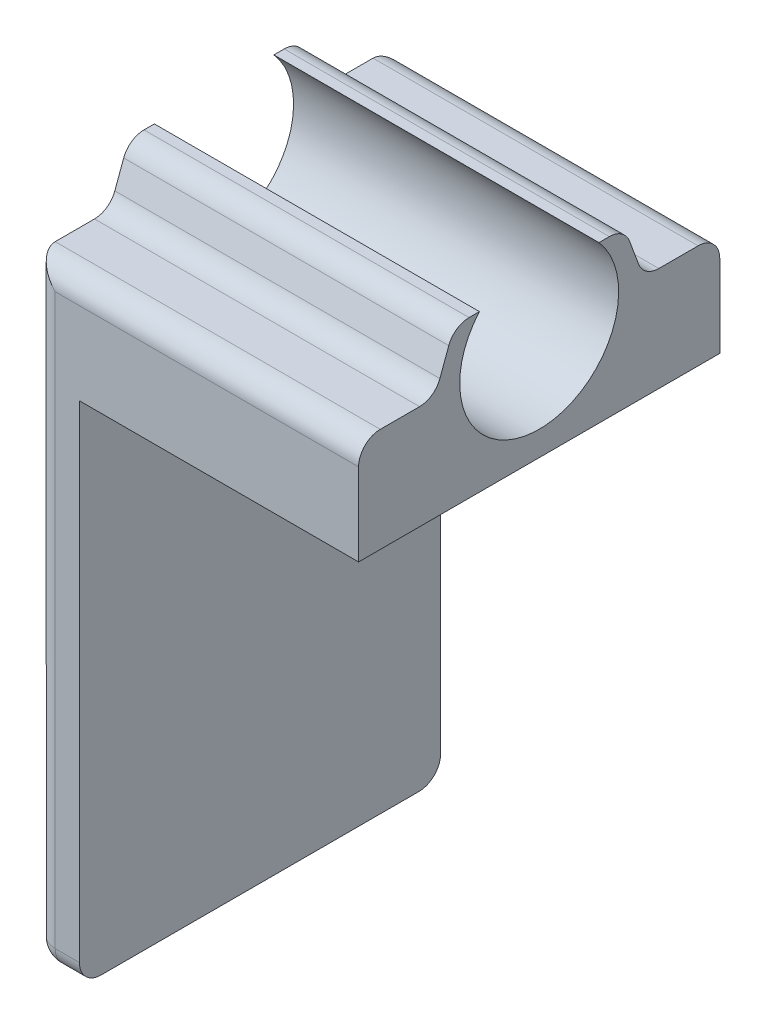
SolidWorks part; units mm, degrees
ref_plane "Front Plane" through (0, 0, 0) normal (0, 0, 1) x (1, 0, 0)
ref_plane "Top Plane" through (0, 0, 0) normal (0, 1, 0) x (1, 0, 0)
ref_plane "Right Plane" through (0, 0, 0) normal (1, 0, 0) x (0, 0, -1)
sketch "Sketch1" plane through (0, 0, 0) normal (0, 1, 0) x (1, 0, 0)
  line L1 (-22.5, -25) -> (22.5, -25)
  line L2 (-22.5, -25) -> (-22.5, 25)
  line L3 (-22.5, 25) -> (22.5, 25)
  line L4 (22.5, -25) -> (22.5, 25)
  line L5 (-22.5, -25) -> (22.5, 25) construction
  line L6 (-22.5, 25) -> (22.5, -25) construction
  point P0 (0, 0)
  dimension "D1" = 45
  dimension "D2" = 50
extrude "Boss-Extrude1" add sketch "Sketch1" along normal blind 92
sketch "Sketch2" plane through (0, 0, -25) normal (0, 0, -1) x (-1, 0, 0)
  line L0 (-22.5, 92) -> (-22.5, 0) construction
  line L1 (-22.5, 0) -> (16.15, 0)
  line L2 (-22.5, 0) -> (-22.5, 70.35)
  line L3 (-22.5, 70.35) -> (16.15, 70.35)
  line L4 (16.15, 0) -> (16.15, 70.35)
  line L5 (-22.5, 0) -> (22.5, 0) construction
  line L6 (22.5, 92) -> (22.5, 0) construction
  dimension "D1" = 0
  dimension "D2" = 6.35
  dimension "D3" = 70.35
sketch "Sketch3" plane through (22.5, 0, 0) normal (1, 0, 0) x (0, 0, -1)
  line L0 (0, 92) -> (0, 77.5) construction
  line L1 (-25, 92) -> (25, 92) construction
  circle A0 centre (0, 84.75) radius 11
  dimension "D1" = 22
  dimension "D2" = 7.25
extrude "Cut-Extrude2" cut sketch "Sketch3" against normal up to surface (45 mm away) up to face at (-22.5, 46, 0)
sketch "Sketch4" plane through (22.5, 0, 0) normal (1, 0, 0) x (0, 0, -1)
  line L0 (11.793, 92) -> (14.47, 84.75)
  line L1 (25, 92) -> (25, 0) construction
  line L2 (25, 84.75) -> (-25, 84.75) construction
  line L3 (-25, 92) -> (-25, 0) construction
  line L4 (8.2727, 92) -> (25, 92) construction
  line L5 (14.47, 84.75) -> (25, 84.75)
  line L6 (25, 84.75) -> (25, 92)
  line L7 (25, 92) -> (11.793, 92)
  line L8 (0, 84.75) -> (0, 92) construction
  line L9 (-25, 84.75) -> (-25, 92)
  line L10 (-14.47, 84.75) -> (-25, 84.75)
  line L11 (-11.793, 92) -> (-14.47, 84.75)
  line L12 (-25, 92) -> (-11.793, 92)
extrude "Cut-Extrude3" cut sketch "Sketch4" against normal up to surface (45 mm away) up to face at (-22.5, 58.2917, 0)
fillet "Fillet5" radius 3 4 edges at (0, 84.75, 14.47) (0, 92, 11.793) (0, 84.75, -14.47) (0, 92, -11.793)
fillet "Fillet6" radius 3 8 edges at (22.5, 0, 0) (0, 0, -25) (0, 0, 25) (-22.5, 0, 0) (0, 84.75, -25) (0, 84.75, 25) (-22.5, 42.375, 25) (-22.5, 42.375, -25)
sketch "Sketch5" plane through (-22.5, 0, 0) normal (-1, 0, 0) x (0, 0, 1)
  line L0 (-19.5199, 8.015) -> (19.2476, 8.015) construction
  text T0 "OneChair V3"
extrude "Cut-Extrude4" cut sketch "Sketch5" against normal blind 1
sketch "Sketch15" plane through (-22.5, 0, 0) normal (-1, 0, 0) x (0, 0, 1)
  line L3 (10.2596, 32.0046) -> (9.9115, 31.8204)
  line L7 (10.2596, 30.9578) -> (10.2596, 30.6198)
  line L10 (12.867, 34.9608) -> (4.2649, 30.6858)
  line L11 (14.52, 34.2529) -> (10.2596, 32.0046)
  line L12 (10.2596, 32.0046) -> (9.9115, 31.8204)
  line L13 (9.9115, 31.8204) -> (-14.2582, 18.9772)
  line L14 (-11.8535, 18.0077) -> (-8.8687, 18.0077)
  line L15 (10.2596, 30.0222) -> (10.2596, 30.9578)
  line L16 (10.828, 30.7106) -> (10.828, 30.7064)
  spline S7 degree 3 poles (-15.2979, 21.0019) (-15.3375, 21.2141) (-15.3567, 21.4299) (-15.3849, 21.6442) knots 29 29 29 29 30 30 30 30
  spline S8 degree 3 poles (-15.1435, 20.3562) (-15.1984, 20.5822) (-15.2583, 20.7902) (-15.2979, 21.0019) knots 28 28 28 28 29 29 29 29
  spline S9 degree 3 poles (-10.0647, 23.0588) (-11.7426, 22.1659) (-13.4314, 21.2673) (-15.1435, 20.3562) knots 27 27 27 27 28 28 28 28
  spline S10 degree 3 poles (-10.1505, 23.6586) (-10.1362, 23.4613) (-10.0952, 23.2658) (-10.0647, 23.0588) knots 26 26 26 26 27 27 27 27
  spline S11 degree 3 poles (-10.0043, 24.7775) (-10.1119, 24.4127) (-10.1781, 24.0401) (-10.1505, 23.6586) knots 25 25 25 25 26 26 26 26
  spline S12 degree 3 poles (-9.1188, 27.7673) (-9.4119, 26.7701) (-9.7102, 25.7744) (-10.0043, 24.7775) knots 24 24 24 24 25 25 25 25
  spline S13 degree 3 poles (-8.585, 28.698) (-8.8238, 28.4241) (-9.0148, 28.1212) (-9.1188, 27.7673) knots 23 23 23 23 24 24 24 24
  spline S14 degree 3 poles (-6.5207, 30.0144) (-7.3559, 29.8102) (-8.0265, 29.3386) (-8.585, 28.698) knots 22 22 22 22 23 23 23 23
  spline S15 degree 3 poles (-5.8867, 30.0896) (-6.0986, 30.0862) (-6.3152, 30.0646) (-6.5207, 30.0144) knots 21 21 21 21 22 22 22 22
  spline S16 degree 3 poles (-3.9427, 30.0956) (-4.5907, 30.095) (-5.2388, 30.0998) (-5.8867, 30.0896) knots 20 20 20 20 21 21 21 21
  spline S17 degree 3 poles (0.0807, 30.0993) (-1.2605, 30.097) (-2.6016, 30.0969) (-3.9427, 30.0956) knots 19 19 19 19 20 20 20 20
  spline S18 degree 3 poles (2.8334, 30.103) (1.916, 30.114) (0.9983, 30.1009) (0.0807, 30.0993) knots 18 18 18 18 19 19 19 19
  spline S19 degree 3 poles (3.4965, 30.2699) (3.284, 30.1558) (3.0781, 30.1) (2.8334, 30.103) knots 17 17 17 17 18 18 18 18
  spline S28 degree 3 poles (-12.5035, 30.7783) (-11.8211, 31.7697) (-10.94, 32.5326) (-9.8566, 33.0581) knots 5 5 5 5 6 6 6 6
  spline S29 degree 3 poles (-13.5209, 28.6858) (-13.2999, 29.4445) (-12.9836, 30.15) (-12.5035, 30.7783) knots 4 4 4 4 5 5 5 5
  spline S30 degree 3 poles (-15.205, 22.9992) (-14.6499, 24.8966) (-14.074, 26.7879) (-13.5209, 28.6858) knots 3 3 3 3 4 4 4 4
  spline S31 degree 3 poles (-15.3675, 22.092) (-15.3147, 22.3949) (-15.2907, 22.706) (-15.205, 22.9992) knots 2 2 2 2 3 3 3 3
  spline S32 degree 3 poles (-15.3849, 22.0015) (-15.3791, 22.0317) (-15.3728, 22.0618) (-15.3675, 22.092) knots 1 1 1 1 2 2 2 2
  spline S33 degree 3 poles (-15.3849, 21.6442) (-15.3849, 21.7633) (-15.3849, 21.8824) (-15.3849, 22.0015) knots 0 0 0 0 1 1 1 1
  spline S35 degree 3 poles (9.9115, 31.8204) (1.8611, 27.5421) (-6.186, 23.2664) (-14.2582, 18.9772) knots 3 3 3 3 4 4 4 4
  spline S36 degree 3 poles (-14.2582, 18.9772) (-14.0985, 18.8485) (-13.9614, 18.7241) (-13.8109, 18.6198) knots 4 4 4 4 5 5 5 5
  spline S37 degree 3 poles (-13.8109, 18.6198) (-13.2728, 18.2448) (-12.6632, 18.08) (-12.0175, 18.0287) knots 5 5 5 5 6 6 6 6
  spline S38 degree 3 poles (-12.0175, 18.0287) (-11.9629, 18.0245) (-11.9082, 18.0144) (-11.8535, 18.0077) knots 6 6 6 6 7 7 7 7
  spline S39 degree 3 poles (-15.3849, 21.6442) (-15.3563, 21.4298) (-15.3378, 21.2137) (-15.2975, 21.0018) knots 9 9 9 9 10 10 10 10
  spline S40 degree 3 poles (-15.2975, 21.0018) (-15.258, 20.7899) (-15.1983, 20.5822) (-15.1436, 20.3561) knots 10 10 10 10 11 11 11 11
  spline S41 degree 3 poles (-15.1436, 20.3561) (-13.4317, 21.2675) (-11.7426, 22.1663) (-10.0643, 23.0584) knots 11 11 11 11 12 12 12 12
  spline S42 degree 3 poles (-10.0643, 23.0584) (-10.0954, 23.2661) (-10.1366, 23.4612) (-10.1501, 23.6588) knots 12 12 12 12 13 13 13 13
  spline S43 degree 3 poles (-10.1501, 23.6588) (-10.1778, 24.0405) (-10.1122, 24.4129) (-10.0046, 24.7779) knots 13 13 13 13 14 14 14 14
  spline S44 degree 3 poles (-10.0046, 24.7779) (-9.7103, 25.7742) (-9.4119, 26.7697) (-9.1184, 27.7669) knots 14 14 14 14 15 15 15 15
  spline S45 degree 3 poles (-9.1184, 27.7669) (-9.015, 28.1209) (-8.8241, 28.4244) (-8.5853, 28.6977) knots 15 15 15 15 16 16 16 16
  spline S46 degree 3 poles (-8.5853, 28.6977) (-8.0262, 29.3384) (-7.3561, 29.8101) (-6.5203, 30.0144) knots 16 16 16 16 17 17 17 17
  spline S47 degree 3 poles (-6.5203, 30.0144) (-6.3152, 30.0648) (-6.0982, 30.0859) (-5.8864, 30.0892) knots 17 17 17 17 18 18 18 18
  spline S48 degree 3 poles (-5.8864, 30.0892) (-5.2389, 30.1002) (-4.5907, 30.0951) (-3.9424, 30.096) knots 18 18 18 18 19 19 19 19
  spline S49 degree 3 poles (-3.9424, 30.096) (-2.6013, 30.0968) (-1.2602, 30.0968) (0.0808, 30.0993) knots 19 19 19 19 20 20 20 20
  spline S50 degree 3 poles (0.0808, 30.0993) (0.9982, 30.101) (1.9163, 30.1144) (2.8336, 30.1027) knots 20 20 20 20 21 21 21 21
  spline S51 degree 3 poles (2.8336, 30.1027) (3.0783, 30.1002) (3.2843, 30.1556) (3.4962, 30.27) knots 21 21 21 21 22 22 22 22
  spline S52 degree 3 poles (3.4962, 30.27) (3.7524, 30.4092) (4.0087, 30.5475) (4.2649, 30.6858) knots 22 22 22 22 23 23 23 23
  spline S62 degree 3 poles (-15.3675, 22.092) (-15.3728, 22.0618) (-15.3791, 22.0317) (-15.3849, 22.0015) knots 9 9 9 9 10 10 10 10
  spline S63 degree 3 poles (-15.205, 22.9992) (-15.2907, 22.706) (-15.3147, 22.3949) (-15.3675, 22.092) knots 8 8 8 8 9 9 9 9
  spline S64 degree 3 poles (-13.5209, 28.6858) (-14.074, 26.7879) (-14.6499, 24.8966) (-15.205, 22.9992) knots 7 7 7 7 8 8 8 8
  spline S65 degree 3 poles (-12.5035, 30.7783) (-12.9836, 30.15) (-13.2999, 29.4445) (-13.5209, 28.6858) knots 6 6 6 6 7 7 7 7
  spline S66 degree 3 poles (-9.8566, 33.0581) (-10.94, 32.5326) (-11.8211, 31.7697) (-12.5035, 30.7783) knots 5 5 5 5 6 6 6 6
  spline S69 degree 3 poles (-8.8687, 18.0077) (-8.8317, 18.0127) (-8.7939, 18.0212) (-8.7569, 18.0212) knots 2 2 2 2 3 3 3 3
  spline S70 degree 3 poles (-8.7569, 18.0212) (-7.4225, 18.0228) (-6.0881, 18.0237) (-4.7538, 18.0254) knots 3 3 3 3 4 4 4 4
  spline S71 degree 3 poles (-4.7538, 18.0254) (-3.3286, 18.027) (-1.9035, 18.0279) (-0.4783, 18.0304) knots 4 4 4 4 5 5 5 5
  spline S72 degree 3 poles (-0.4783, 18.0304) (0.4987, 18.0321) (1.4757, 18.0338) (2.4527, 18.0388) knots 5 5 5 5 6 6 6 6
  spline S73 degree 3 poles (2.4527, 18.0388) (2.9118, 18.0413) (3.344, 18.175) (3.7627, 18.3491) knots 6 6 6 6 7 7 7 7
  spline S74 degree 3 poles (3.7627, 18.3491) (5.2963, 18.9872) (6.5576, 19.9735) (7.5253, 21.3255) knots 7 7 7 7 8 8 8 8
  spline S75 degree 3 poles (7.5253, 21.3255) (7.9466, 21.9132) (8.1921, 22.5808) (8.393, 23.272) knots 8 8 8 8 9 9 9 9
  spline S76 degree 3 poles (8.393, 23.272) (8.7991, 24.6694) (9.2229, 26.0618) (9.6341, 27.4575) knots 9 9 9 9 10 10 10 10
  spline S77 degree 3 poles (9.6341, 27.4575) (9.8098, 28.052) (9.9788, 28.6472) (10.1352, 29.2467) knots 10 10 10 10 11 11 11 11
  spline S78 degree 3 poles (10.1352, 29.2467) (10.1924, 29.4653) (10.2066, 29.6949) (10.2403, 29.9202) knots 11 11 11 11 12 12 12 12
  spline S79 degree 3 poles (10.2403, 29.9202) (10.2453, 29.9505) (10.2529, 29.9799) (10.2596, 30.0102) knots 12 12 12 12 13 13 13 13
  spline S80 degree 3 poles (-3.0486, 22.1503) (-0.3135, 24.0615) (2.4216, 25.9735) (5.1845, 27.9048) knots 8 8 8 8 9 9 9 9
  spline S81 degree 3 poles (-3.0369, 22.1293) (-3.0411, 22.1361) (-3.0444, 22.1428) (-3.0486, 22.1503) knots 7 7 7 7 8 8 8 8
  spline S82 degree 3 poles (-2.9957, 22.1276) (-3.0091, 22.1276) (-3.0234, 22.1285) (-3.0369, 22.1293) knots 6 6 6 6 7 7 7 7
  spline S83 degree 3 poles (1.2899, 22.1361) (-0.1386, 22.1243) (-1.5671, 22.1293) (-2.9957, 22.1276) knots 5 5 5 5 6 6 6 6
  spline S84 degree 3 poles (3.2196, 22.8306) (2.6587, 22.3774) (2.0088, 22.1428) (1.2899, 22.1361) knots 4 4 4 4 5 5 5 5
  spline S85 degree 3 poles (4.057, 24.0926) (3.8897, 23.6016) (3.629, 23.161) (3.2196, 22.8306) knots 3 3 3 3 4 4 4 4
  spline S86 degree 3 poles (4.4757, 25.4572) (4.3395, 25.0015) (4.21, 24.5424) (4.057, 24.0926) knots 2 2 2 2 3 3 3 3
  spline S87 degree 3 poles (5.145, 27.7106) (4.9222, 26.9598) (4.7002, 26.2081) (4.4757, 25.4572) knots 1 1 1 1 2 2 2 2
  spline S88 degree 3 poles (5.1845, 27.9048) (5.1677, 27.8207) (5.1601, 27.7644) (5.145, 27.7106) knots 0 0 0 0 1 1 1 1
  spline S93 degree 3 poles (-9.8566, 33.0581) (-9.2168, 33.6509) (-5.7863, 34.9432) (-4.9354, 35.2913) knots 5 5 5 5 6 6 6 6
  spline S94 degree 3 poles (-4.9354, 35.2913) (-4.0778, 35.6427) (-3.1823, 35.9) (-2.3071, 36.2086) knots 6 6 6 6 7 7 7 7
  spline S95 degree 3 poles (-2.3071, 36.2086) (-2.1599, 36.2607) (-1.9985, 36.3372) (-1.8984, 36.4499) knots 7 7 7 7 8 8 8 8
  spline S96 degree 3 poles (-1.8984, 36.4499) (-0.4228, 38.1197) (1.0444, 39.7972) (2.5124, 41.4729) knots 8 8 8 8 9 9 9 9
  spline S97 degree 3 poles (2.5124, 41.4729) (2.5385, 41.5031) (2.5604, 41.5368) (2.5957, 41.5847) knots 9 9 9 9 10 10 10 10
  spline S98 degree 3 poles (2.5957, 41.5847) (2.5309, 41.6301) (2.4754, 41.6738) (2.4158, 41.7091) knots 10 10 10 10 11 11 11 11
  spline S99 degree 3 poles (2.4158, 41.7091) (1.659, 42.1607) (0.8989, 42.6063) (0.1489, 43.067) knots 11 11 11 11 12 12 12 12
  spline S100 degree 3 poles (0.1489, 43.067) (-0.0091, 43.1637) (-0.0983, 43.1419) (-0.2269, 43.025) knots 12 12 12 12 13 13 13 13
  spline S101 degree 3 poles (-0.2269, 43.025) (-1.2233, 42.1195) (-2.2255, 41.219) (-3.2294, 40.321) knots 13 13 13 13 14 14 14 14
  spline S102 degree 3 poles (-3.2294, 40.321) (-4.1745, 39.476) (-5.6005, 39.687) (-6.1949, 40.7548) knots 14 14 14 14 15 15 15 15
  spline S103 degree 3 poles (-6.1949, 40.7548) (-6.6128, 41.5057) (-6.4665, 42.5155) (-5.8216, 43.0881) knots 15 15 15 15 16 16 16 16
  spline S104 degree 3 poles (-5.8216, 43.0881) (-4.3637, 44.3837) (-2.8788, 45.65) (-1.4351, 46.9616) knots 16 16 16 16 17 17 17 17
  spline S105 degree 3 poles (-1.4351, 46.9616) (-0.9517, 47.4006) (0.117, 47.4703) (0.6484, 47.1441) knots 17 17 17 17 18 18 18 18
  spline S106 degree 3 poles (0.6484, 47.1441) (1.9474, 46.3462) (3.2759, 45.5953) (4.5918, 44.8252) knots 18 18 18 18 19 19 19 19
  spline S107 degree 3 poles (4.5918, 44.8252) (6.1615, 43.9079) (7.7187, 42.9653) (9.307, 42.0816) knots 19 19 19 19 20 20 20 20
  spline S108 degree 3 poles (9.307, 42.0816) (10.2016, 41.583) (10.3933, 40.6615) (10.3025, 39.9687) knots 20 20 20 20 21 21 21 21
  spline S109 degree 3 poles (10.3025, 39.9687) (10.2436, 39.5146) (10.0637, 39.1169) (9.7526, 38.7655) knots 21 21 21 21 22 22 22 22
  spline S110 degree 3 poles (9.7526, 38.7655) (8.6167, 37.4816) (7.495, 36.1851) (6.3692, 34.8936) knots 22 22 22 22 23 23 23 23
  spline S111 degree 3 poles (6.3692, 34.8936) (6.312, 34.828) (6.2582, 34.7591) (6.1657, 34.6464) knots 23 23 23 23 24 24 24 24
  spline S112 degree 3 poles (6.1657, 34.6464) (6.2927, 34.6321) (6.3675, 34.6119) (6.4407, 34.6161) knots 24 24 24 24 25 25 25 25
  spline S113 degree 3 poles (6.4407, 34.6161) (8.5191, 34.7271) (10.5976, 34.8322) (12.6752, 34.9566) knots 25 25 25 25 26 26 26 26
  spline S114 degree 3 poles (12.6752, 34.9566) (12.74, 34.9608) (12.8047, 34.9617) (12.867, 34.9608) knots 26 26 26 26 27 27 27 27
  spline S115 degree 3 poles (14.8496, 33.4566) (14.7857, 33.7627) (14.6738, 34.0301) (14.52, 34.2529) knots 0 0 0 0 1 1 1 1
  spline S116 degree 3 poles (-14.2582, 18.9772) (-14.0985, 18.8485) (-13.9614, 18.7241) (-13.8109, 18.6198) knots 4 4 4 4 5 5 5 5
  spline S117 degree 3 poles (-13.8109, 18.6198) (-13.2728, 18.2448) (-12.6632, 18.08) (-12.0175, 18.0287) knots 5 5 5 5 6 6 6 6
  spline S118 degree 3 poles (-12.0175, 18.0287) (-11.9629, 18.0245) (-11.9082, 18.0144) (-11.8535, 18.0077) knots 6 6 6 6 7 7 7 7
  spline S119 degree 3 poles (-8.8687, 18.0077) (-8.8317, 18.0127) (-8.7939, 18.0212) (-8.7569, 18.0212) knots 8 8 8 8 9 9 9 9
  spline S120 degree 3 poles (-8.7569, 18.0212) (-7.4225, 18.0228) (-6.0881, 18.0237) (-4.7538, 18.0254) knots 9 9 9 9 10 10 10 10
  spline S121 degree 3 poles (-4.7538, 18.0254) (-3.3286, 18.027) (-1.9035, 18.0279) (-0.4783, 18.0304) knots 10 10 10 10 11 11 11 11
  spline S122 degree 3 poles (-0.4783, 18.0304) (0.4987, 18.0321) (1.4757, 18.0338) (2.4527, 18.0388) knots 11 11 11 11 12 12 12 12
  spline S123 degree 3 poles (2.4527, 18.0388) (2.9118, 18.0413) (3.344, 18.175) (3.7627, 18.3491) knots 12 12 12 12 13 13 13 13
  spline S124 degree 3 poles (3.7627, 18.3491) (5.2963, 18.9872) (6.5576, 19.9735) (7.5253, 21.3255) knots 13 13 13 13 14 14 14 14
  spline S125 degree 3 poles (7.5253, 21.3255) (7.9466, 21.9132) (8.1921, 22.5808) (8.393, 23.272) knots 14 14 14 14 15 15 15 15
  spline S126 degree 3 poles (8.393, 23.272) (8.7991, 24.6694) (9.2229, 26.0618) (9.6341, 27.4575) knots 15 15 15 15 16 16 16 16
  spline S127 degree 3 poles (9.6341, 27.4575) (9.8098, 28.052) (9.9788, 28.6472) (10.1352, 29.2467) knots 16 16 16 16 17 17 17 17
  spline S128 degree 3 poles (10.1352, 29.2467) (10.1924, 29.4653) (10.2066, 29.6949) (10.2403, 29.9202) knots 17 17 17 17 18 18 18 18
  spline S129 degree 3 poles (10.2403, 29.9202) (10.2447, 29.9466) (10.251, 29.9722) (10.257, 29.9984) knots 18 18 18 18 19 19 19 19
  spline S130 degree 3 poles (10.257, 29.9984) (10.2587, 30.0062) (10.2596, 30.0142) (10.2596, 30.0222) knots 19 19 19 19 20 20 20 20
  spline S131 degree 3 poles (10.2596, 30.9578) (10.2596, 31.0378) (10.322, 31.1039) (10.4019, 31.1082) knots 21 21 21 21 22 22 22 22
  spline S132 degree 3 poles (10.4019, 31.1082) (10.4037, 31.1083) (10.4055, 31.1084) (10.4073, 31.1085) knots 22 22 22 22 23 23 23 23
  spline S133 degree 3 poles (10.4073, 31.1085) (10.6357, 31.1211) (10.828, 30.9394) (10.828, 30.7106) knots 23 23 23 23 24 24 24 24
  spline S134 degree 3 poles (10.828, 30.7064) (10.7683, 29.9169) (10.7078, 29.1282) (10.6481, 28.3387) knots 25 25 25 25 26 26 26 26
  spline S135 degree 3 poles (10.6481, 28.3387) (10.527, 26.7109) (10.416, 25.0822) (10.2798, 23.4561) knots 26 26 26 26 27 27 27 27
  spline S136 degree 3 poles (10.2798, 23.4561) (10.2277, 22.8331) (10.453, 22.3193) (10.8734, 21.9132) knots 27 27 27 27 28 28 28 28
  spline S137 degree 3 poles (10.8734, 21.9132) (11.8689, 20.9514) (13.6792, 21.4987) (13.9718, 22.8491) knots 28 28 28 28 29 29 29 29
  spline S138 degree 3 poles (13.9718, 22.8491) (14.0752, 23.3241) (14.0844, 23.8202) (14.1248, 24.307) knots 29 29 29 29 30 30 30 30
  spline S139 degree 3 poles (14.1248, 24.307) (14.2492, 25.7952) (14.3661, 27.2843) (14.488, 28.7725) knots 30 30 30 30 31 31 31 31
  spline S140 degree 3 poles (14.488, 28.7725) (14.6099, 30.2608) (14.7344, 31.749) (14.8563, 33.238) knots 31 31 31 31 32 32 32 32
  spline S141 degree 3 poles (14.8563, 33.238) (14.8622, 33.3103) (14.8639, 33.386) (14.8496, 33.4566) knots 32 32 32 32 33 33 33 33
  spline S142 degree 3 poles (4.057, 24.0926) (3.8897, 23.6016) (3.629, 23.161) (3.2196, 22.8306) knots 8 8 8 8 9 9 9 9
  spline S143 degree 3 poles (4.4757, 25.4572) (4.3395, 25.0015) (4.21, 24.5424) (4.057, 24.0926) knots 7 7 7 7 8 8 8 8
  spline S144 degree 3 poles (5.145, 27.7106) (4.9222, 26.9598) (4.7002, 26.2081) (4.4757, 25.4572) knots 6 6 6 6 7 7 7 7
  spline S145 degree 3 poles (5.1845, 27.9048) (5.1677, 27.8207) (5.1601, 27.7644) (5.145, 27.7106) knots 5 5 5 5 6 6 6 6
  spline S146 degree 3 poles (-3.0486, 22.1503) (-0.3135, 24.0615) (2.4216, 25.9735) (5.1845, 27.9048) knots 4 4 4 4 5 5 5 5
  spline S147 degree 3 poles (-3.0369, 22.1293) (-3.0411, 22.1361) (-3.0444, 22.1428) (-3.0486, 22.1503) knots 3 3 3 3 4 4 4 4
  spline S148 degree 3 poles (-2.9957, 22.1276) (-3.0091, 22.1276) (-3.0234, 22.1285) (-3.0369, 22.1293) knots 2 2 2 2 3 3 3 3
  spline S149 degree 3 poles (1.2899, 22.1361) (-0.1386, 22.1243) (-1.5671, 22.1293) (-2.9957, 22.1276) knots 1 1 1 1 2 2 2 2
  spline S150 degree 3 poles (3.2196, 22.8306) (2.6587, 22.3774) (2.0088, 22.1428) (1.2899, 22.1361) knots 0 0 0 0 1 1 1 1
  spline S158 degree 3 poles (7.5381, 45.8286) (7.5373, 47.5059) (9.0149, 48.9528) (10.725, 48.9493) knots 3 3 3 3 4 4 4 4
  spline S159 degree 3 poles (10.7155, 42.5606) (8.9098, 42.5606) (7.539, 43.9705) (7.5381, 45.8286) knots 2 2 2 2 3 3 3 3
  spline S160 degree 3 poles (13.8947, 45.7198) (13.8872, 44.0064) (12.4322, 42.5606) (10.7155, 42.5606) knots 1 1 1 1 2 2 2 2
  spline S161 degree 3 poles (10.725, 48.9493) (12.4988, 48.9457) (13.9025, 47.5155) (13.8947, 45.7198) knots 0 0 0 0 1 1 1 1
extrude "Cut-Extrude6" cut sketch "Sketch15" against normal blind 1 contours S114 S113 S112 S111 S110 S109 S108 S107 S106 S105 S104 S103 S102 S101 S100 S99 S98 S97 S96 S95 S94 S93 S28 S29 S30 S31 S32 S33 S39 S7 S40 S8 S9 S41 S10 S42 S11 S43 S44 S12 S13 S45 S46 S14 S15 S16 | S161 S158 S159 S160 | S140 S141 S115 L11 L3 S35 S36 S37 S38 L14 S69 S70 S71 S72 S73 S74 S75 S76 S77 S78 S79 S130 L15 L7 S131 S132 S133 L16 S134 S135 S136 S137 S138 S139 S80 S88 S87 S86 S85 S84 S83 S82 S81
extrude "Cut-Extrude8" cut sketch "Sketch2" against normal through all
